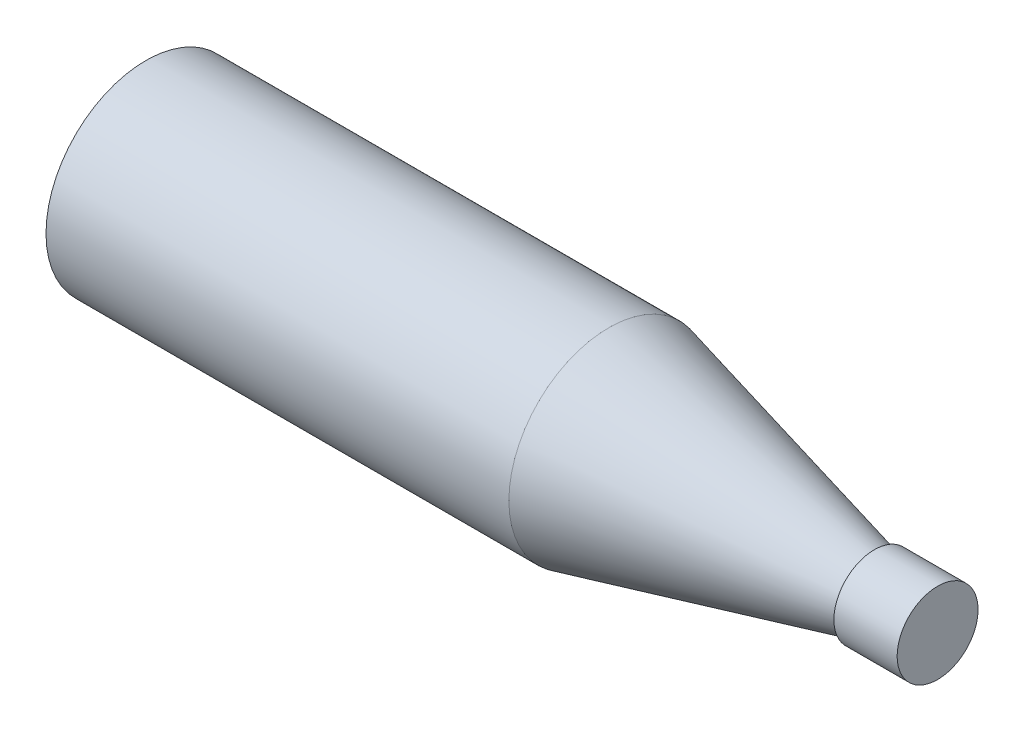
SolidWorks part; units mm, degrees
ref_plane "Спереди" through (0, 0, 0) normal (0, 0, 1) x (1, 0, 0)
ref_plane "Сверху" through (0, 0, 0) normal (0, 1, 0) x (1, 0, 0)
ref_plane "Справа" through (0, 0, 0) normal (1, 0, 0) x (0, 0, -1)
sketch "Эскиз1" plane through (0, 0, 0) normal (0, 0, 1) x (1, 0, 0)
  line L0 (-50.7749, 0) -> (101.9877, 0) construction
  line L1 (-50.7749, 0) -> (-50.7749, 39.5)
  line L2 (-50.7749, 39.5) -> (132.2251, 39.5)
  line L3 (132.2251, 39.5) -> (237.2251, 13.5)
  line L4 (237.2251, 13.5) -> (237.2251, 16)
  line L5 (237.2251, 16) -> (262.2251, 16)
  line L6 (262.2251, 16) -> (262.2251, 0)
  line L7 (-50.7749, 0) -> (262.2251, 0)
  point P8 (262.2251, 8)
  dimension "D1" = 79
  dimension "D2" = 27
  dimension "D3" = 32
  dimension "D4" = 25
  dimension "D5" = 313
  dimension "D6" = 130
revolve "Повернуть2" add sketch "Эскиз1" angle 360 about L0
